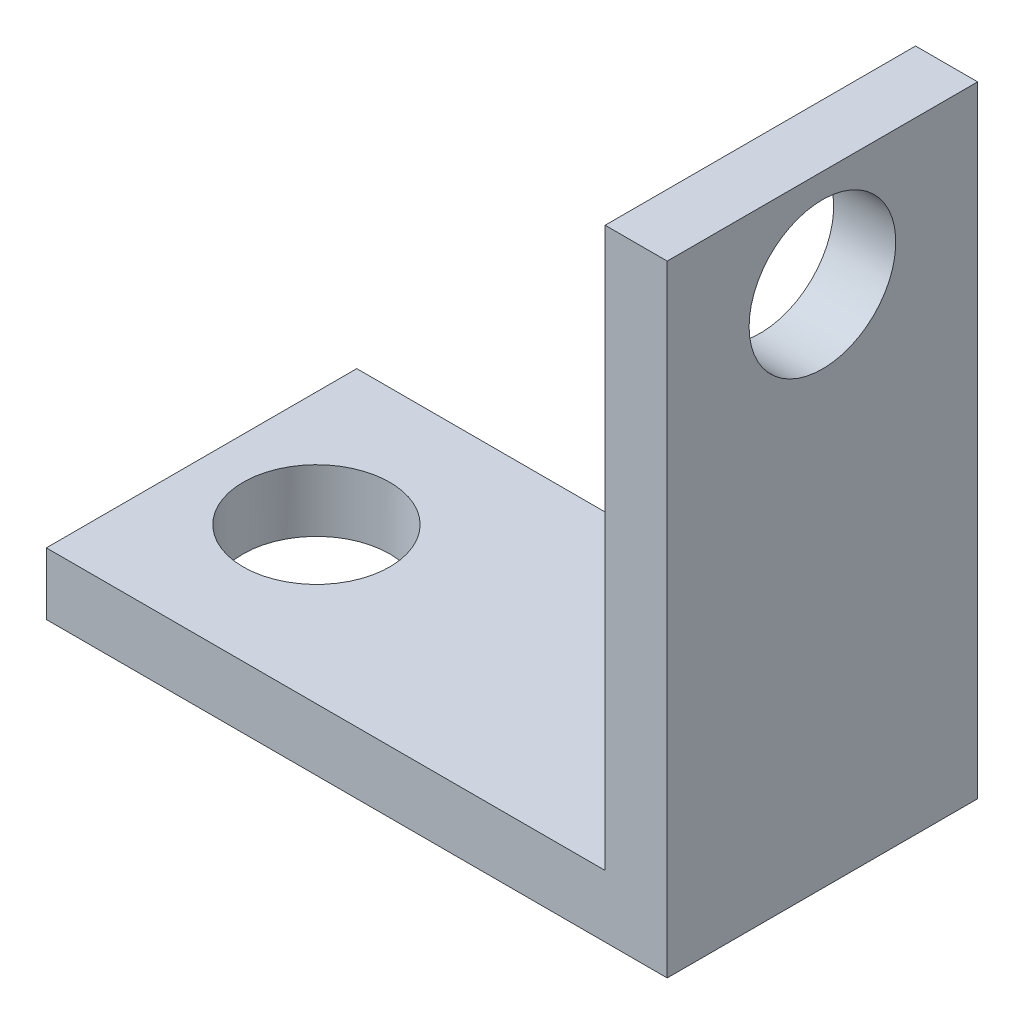
SolidWorks part; units mm, degrees
material "ABS"
ref_plane "Front Plane" through (0, 0, 0) normal (0, 0, 1) x (1, 0, 0)
ref_plane "Top Plane" through (0, 0, 0) normal (0, 1, 0) x (1, 0, 0)
ref_plane "Right Plane" through (0, 0, 0) normal (1, 0, 0) x (0, 0, -1)
sketch "Sketch1" plane through (0, 0, 0) normal (0, 1, 0) x (1, 0, 0)
  line L1 (12.7, 6.35) -> (-12.7, 6.35)
  line L2 (12.7, 6.35) -> (12.7, -6.35)
  line L3 (12.7, -6.35) -> (-12.7, -6.35)
  line L4 (-12.7, 6.35) -> (-12.7, -6.35)
  line L5 (12.7, 6.35) -> (-12.7, -6.35) construction
  line L6 (12.7, -6.35) -> (-12.7, 6.35) construction
  point P0 (0, 0)
  dimension "D1" = 25.4
  dimension "D2" = 12.7
extrude "Boss-Extrude1" add sketch "Sketch1" along normal blind 2.54
sketch "Sketch2" plane through (0, 2.54, 0) normal (0, 1, 0) x (1, 0, 0)
  line L0 (-12.7, -6.35) -> (12.7, -6.35) construction
  line L1 (12.7, 6.35) -> (10.16, 6.35)
  line L2 (12.7, 6.35) -> (12.7, -6.35)
  line L3 (12.7, -6.35) -> (10.16, -6.35)
  line L4 (10.16, 6.35) -> (10.16, -6.35)
  dimension "D1" = 2.54
extrude "Boss-Extrude2" add sketch "Sketch2" along normal blind 22.86
sketch "Sketch3" plane through (0, 2.54, 0) normal (0, 1, 0) x (1, 0, 0)
  line L0 (-8, 0) -> (0, 0) construction
  circle A0 centre (-8, 0) radius 3
  dimension "D1" = 6
  dimension "D2" = 8
extrude "Cut-Extrude1" cut sketch "Sketch3" against normal blind 22.86
sketch "Sketch4" plane through (10.16, 0, 0) normal (-1, 0, 0) x (0, 0, 1)
  line L0 (0, 21.4) -> (0, 0) construction
  line L1 (-6.35, 25.4) -> (6.35, 25.4) construction
  circle A0 centre (0, 21.4) radius 3
  point P6 (0, 25.4)
  dimension "D2" = 6
  dimension "D1" = 4
extrude "Cut-Extrude2" cut sketch "Sketch4" against normal blind 22.86
